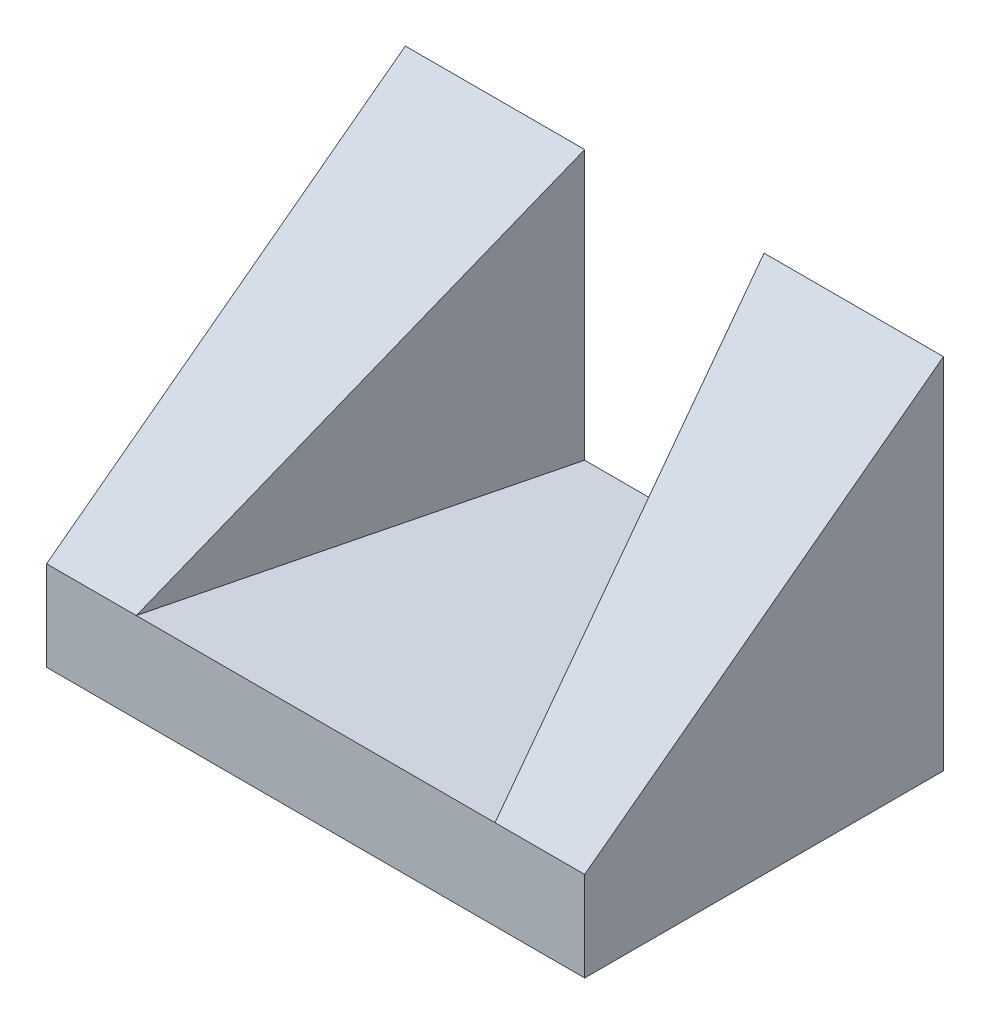
SolidWorks part; units mm, degrees
material "Aleación 6061"
ref_plane "Alzado" through (0, 0, 0) normal (0, 0, 1) x (1, 0, 0)
ref_plane "Planta" through (0, 0, 0) normal (0, 1, 0) x (1, 0, 0)
ref_plane "Vista lateral" through (0, 0, 0) normal (1, 0, 0) x (0, 0, -1)
sketch "Croquis1" plane through (0, 0, 0) normal (0, 1, 0) x (1, 0, 0)
  line L1 (0, 0) -> (60, 0)
  line L2 (0, 0) -> (0, 40)
  line L3 (0, 40) -> (60, 40)
  line L4 (60, 0) -> (60, 40)
  dimension "D1" = 60
  dimension "D2" = 40
extrude "Saliente-Extruir1" add sketch "Croquis1" along normal blind 10
sketch "Croquis2" plane through (0, 10, 0) normal (0, 1, 0) x (1, 0, 0)
  line L0 (0, 0) -> (0, 40)
  line L1 (0, 40) -> (20, 40)
  line L2 (60, 40) -> (0, 40) construction
  line L3 (0, 0) -> (10, 0)
  line L4 (0, 0) -> (60, 0) construction
  line L5 (20, 40) -> (10, 0)
  line L7 (60, 40) -> (40, 40)
  line L8 (60, 0) -> (60, 40)
  line L9 (60, 0) -> (50, 0)
  line L10 (40, 40) -> (50, 0)
extrude "Saliente-Extruir2" add sketch "Croquis2" along normal blind 30
sketch "Croquis3" plane through (60, 0, 0) normal (1, 0, 0) x (0, 0, -1)
  line L0 (0, 0) -> (0, 10)
  line L1 (0, 40) -> (0, 0) construction
  line L2 (0, 10) -> (40, 40)
  line L3 (0, 10) -> (0, 40)
  line L4 (0, 40) -> (40, 40)
  line M7 (40, 40) -> (0, 40)
  line M8 (0, 40) -> (0, 0)
extrude "Cortar-Extruir1" cut sketch "Croquis3" against normal blind 66 and the other way blind 9 contours L2 M8 M7
